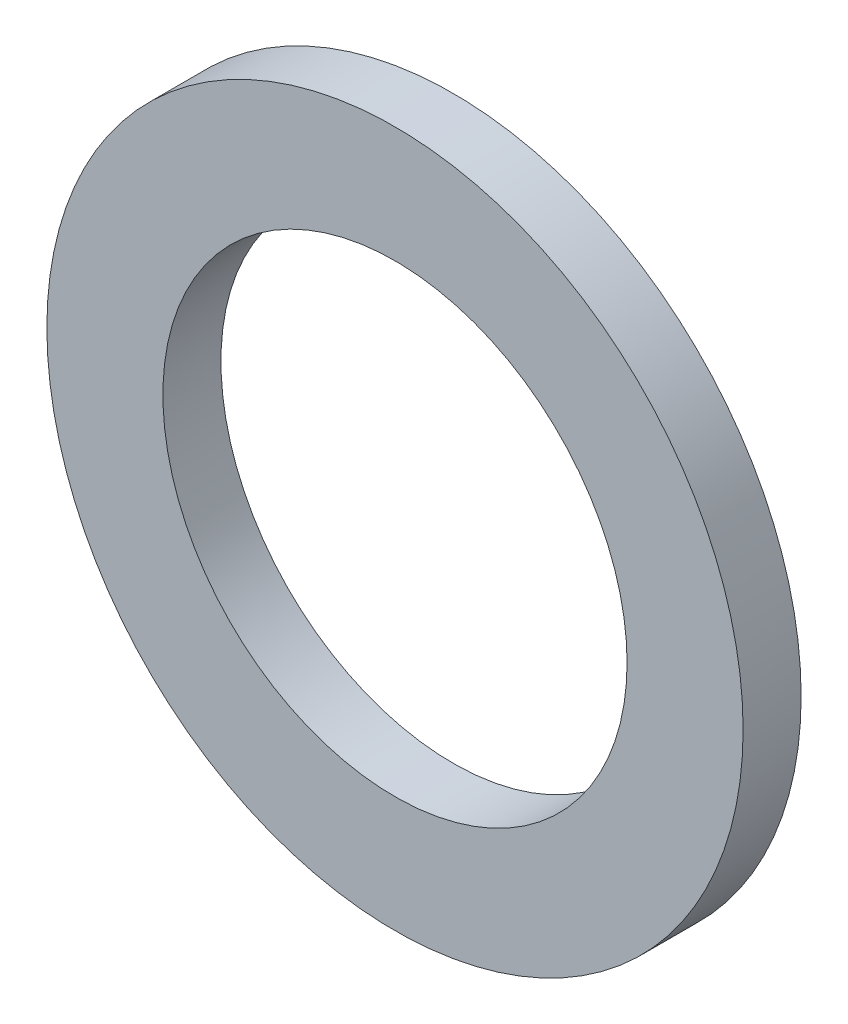
SolidWorks part; units mm, degrees
ref_plane "Alzado" through (0, 0, 0) normal (0, 0, 1) x (1, 0, 0)
ref_plane "Planta" through (0, 0, 0) normal (0, 1, 0) x (1, 0, 0)
ref_plane "Vista lateral" through (0, 0, 0) normal (1, 0, 0) x (0, 0, -1)
sketch "Croquis1" plane through (0, 0, 0) normal (0, 0, 1) x (1, 0, 0)
  circle A0 centre (0, 0) radius 12.7
  circle A1 centre (0, 0) radius 19.05
  dimension "D1" = 25.4
  dimension "D2" = 38.1
extrude "Saliente-Extruir1" add sketch "Croquis1" along normal blind 3.175
